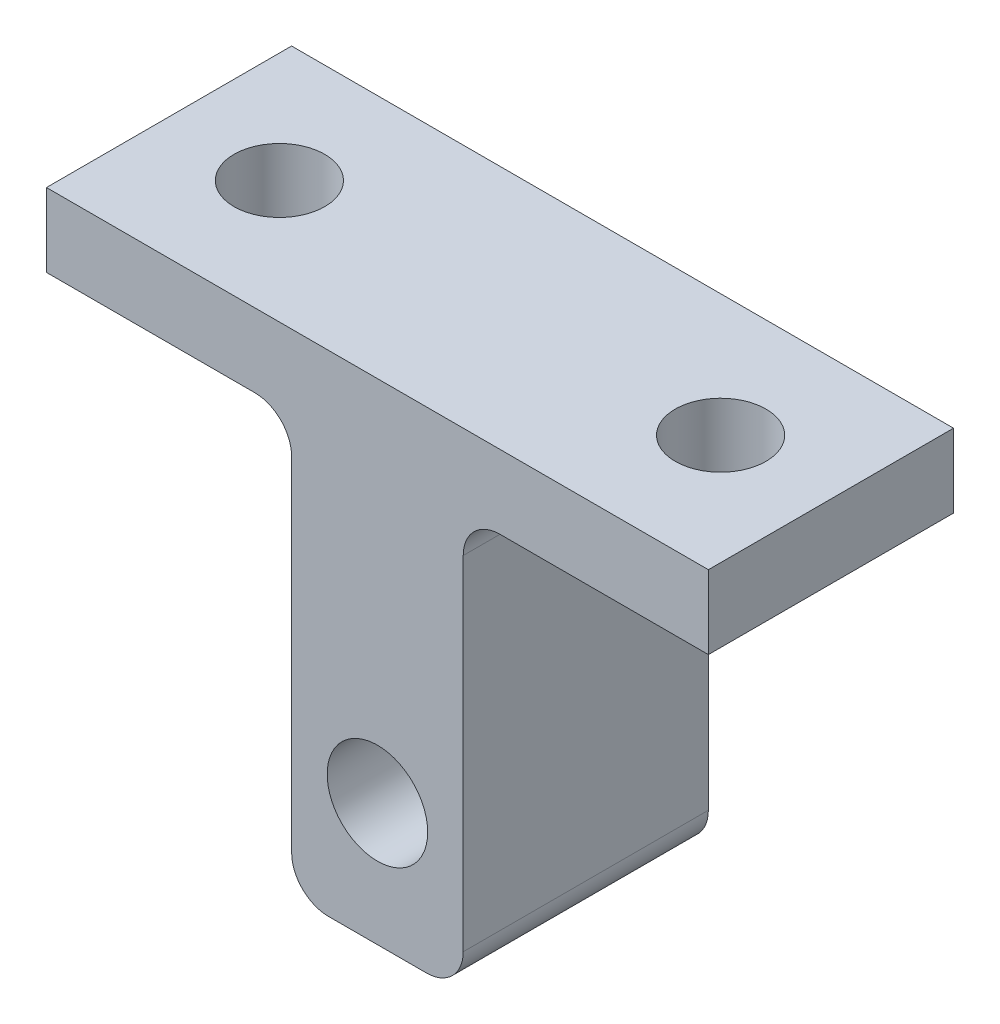
SolidWorks part; units mm, degrees
ref_plane "Front Plane" through (0, 0, 0) normal (0, 0, 1) x (1, 0, 0)
ref_plane "Top Plane" through (0, 0, 0) normal (0, 1, 0) x (1, 0, 0)
ref_plane "Right Plane" through (0, 0, 0) normal (1, 0, 0) x (0, 0, -1)
sketch "Sketch1" plane through (0, 0, 0) normal (0, 0, 1) x (1, 0, 0)
  line L0 (-13.5024, 0) -> (-3.5, 0)
  line L1 (-3.5, 0) -> (-3.5, -17)
  line L2 (-3.5, -17) -> (3.5, -17)
  line L3 (3.5, -17) -> (3.5, 0)
  line L4 (3.5, 0) -> (13.5024, 0)
  line L5 (-13.5024, 0) -> (-13.5024, 3)
  line L6 (-13.5024, 3) -> (13.5024, 3)
  line L7 (13.5024, 3) -> (13.5024, 0)
  circle A0 centre (0, -12) radius 2.05
  point P10 (0, -17)
  point P12 (0, 3)
  dimension "D3" = 4.1
  dimension "D1" = 17
  dimension "D2" = 7
  dimension "D4" = 3
  dimension "D5" = 15
  dimension "D6" = 27.0048
extrude "Boss-Extrude1" add sketch "Sketch1" along normal mid plane 10
fillet "Fillet1" radius 1.5 4 edges at (3.5, 0, 0) (-3.5, -17, 0) (3.5, -17, 0) (-3.5, 0, 0)
sketch "Sketch2" plane through (0, 3, 0) normal (0, 1, 0) x (1, 0, 0)
  line L0 (-9, 0) -> (9, 0) construction
  line L2 (-13.5024, -5) -> (-13.5024, 5) construction
  circle A0 centre (-9, 0) radius 1.85
  circle A1 centre (9, 0) radius 1.85
  point P4 (0, 0)
  point P7 (-13.5024, 0)
  dimension "D1" = 18
  dimension "D2" = 3.7
extrude "Cut-Extrude1" cut sketch "Sketch2" against normal through all
